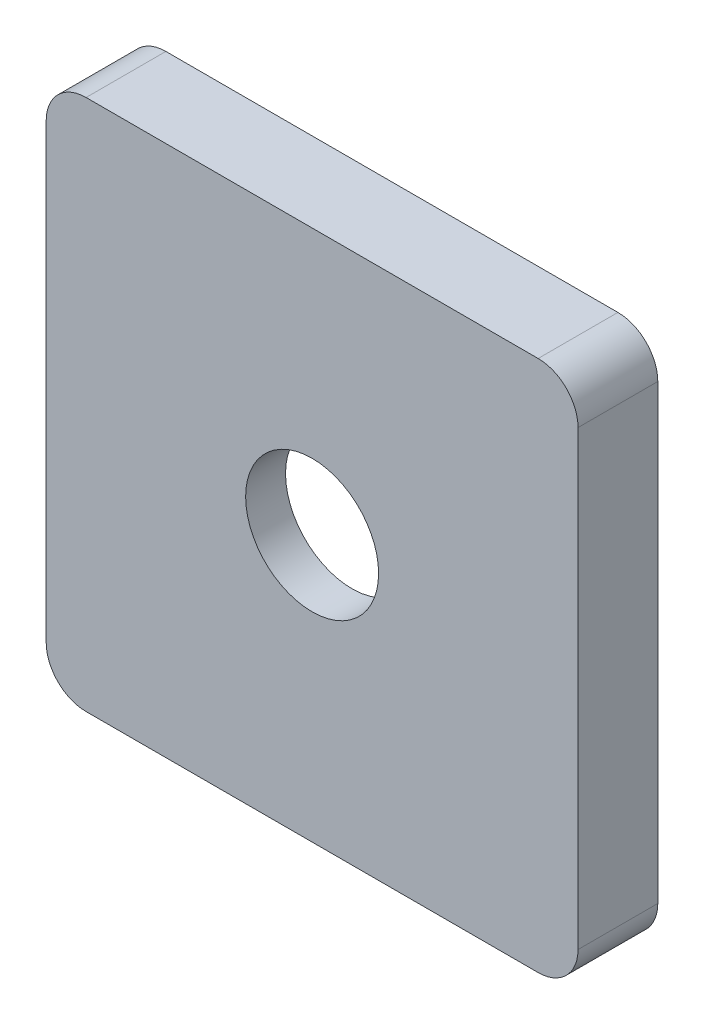
SolidWorks part; units mm, degrees
ref_plane "Front Plane" through (0, 0, 0) normal (0, 0, 1) x (1, 0, 0)
ref_plane "Top Plane" through (0, 0, 0) normal (0, 1, 0) x (1, 0, 0)
ref_plane "Right Plane" through (0, 0, 0) normal (1, 0, 0) x (0, 0, -1)
sketch "Sketch1" plane through (0, 0, 0) normal (0, 0, 1) x (1, 0, 0)
  line L1 (-8.5, 10) -> (8.5, 10)
  line L2 (-10, 8.5) -> (-10, -8.5)
  line L3 (-8.5, -10) -> (8.5, -10)
  line L4 (10, 8.5) -> (10, -8.5)
  line L5 (-10, 10) -> (10, -10) construction
  line L6 (-10, -10) -> (10, 10) construction
  circle A0 centre (0, 0) radius 2.5
  arc A1 (-10, -8.5) -> (-8.5, -10) centre (-8.5, -8.5) ccw
  arc A2 (8.5, -10) -> (10, -8.5) centre (8.5, -8.5) ccw
  arc A3 (8.5, 10) -> (10, 8.5) centre (8.5, 8.5) cw
  arc A4 (-8.5, 10) -> (-10, 8.5) centre (-8.5, 8.5) ccw
  point P0 (0, 0)
  dimension "D3" = 5
  dimension "D4" = 1.5
  dimension "D1" = 20
  dimension "D2" = 20
extrude "Boss-Extrude1" add sketch "Sketch1" along normal mid plane 3
sketch "Sketch2" plane through (0, 0, -1.5) normal (0, 0, -1) x (-1, 0, 0)
  circle A0 centre (0, 0) radius 5
  dimension "D1" = 10
extrude "Cut-Extrude1" cut sketch "Sketch2" against normal blind 1.5
